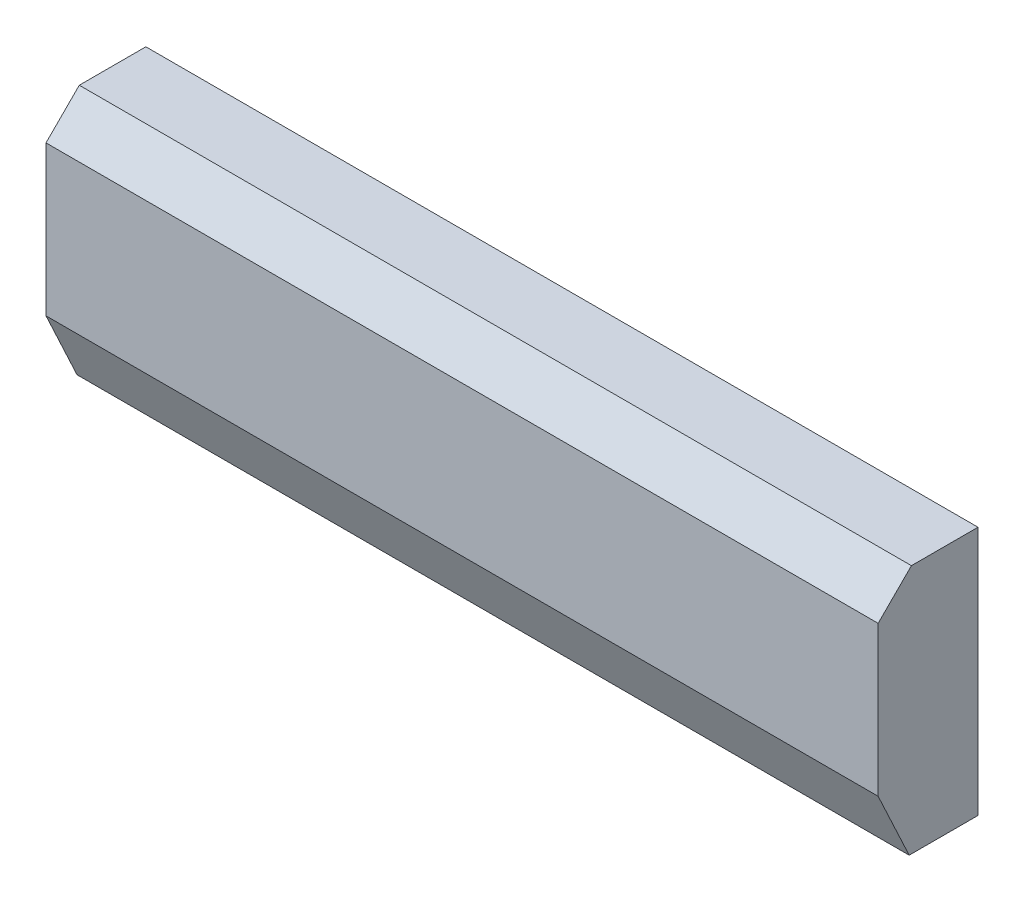
SolidWorks part; units mm, degrees
material "Стекло"
ref_plane "Front" through (0, 0, 0) normal (0, 0, 1) x (1, 0, 0)
ref_plane "Top" through (0, 0, 0) normal (0, 1, 0) x (1, 0, 0)
ref_plane "Right" through (0, 0, 0) normal (1, 0, 0) x (0, 0, -1)
sketch "Эскиз1" plane through (0, 0, 0) normal (0, 0, 1) x (1, 0, 0)
  line L1 (-12.5, -3.5) -> (12.5, -3.5)
  line L2 (-12.5, -3.5) -> (-12.5, 4)
  line L3 (-12.5, 4) -> (12.5, 4)
  line L4 (12.5, -3.5) -> (12.5, 4)
  dimension "D1" = 25
  dimension "D2" = 7.5
  dimension "D3" = 3.5
  dimension "D4" = 12.5
extrude "Вытянуть1" add sketch "Эскиз1" along normal blind 3
chamfer "Фаска1" distance 1 angle 45 1 edges at (0, 4, 3)
chamfer "Фаска2" distance 2 angle 25 1 edges at (0, -3.5, 3)
